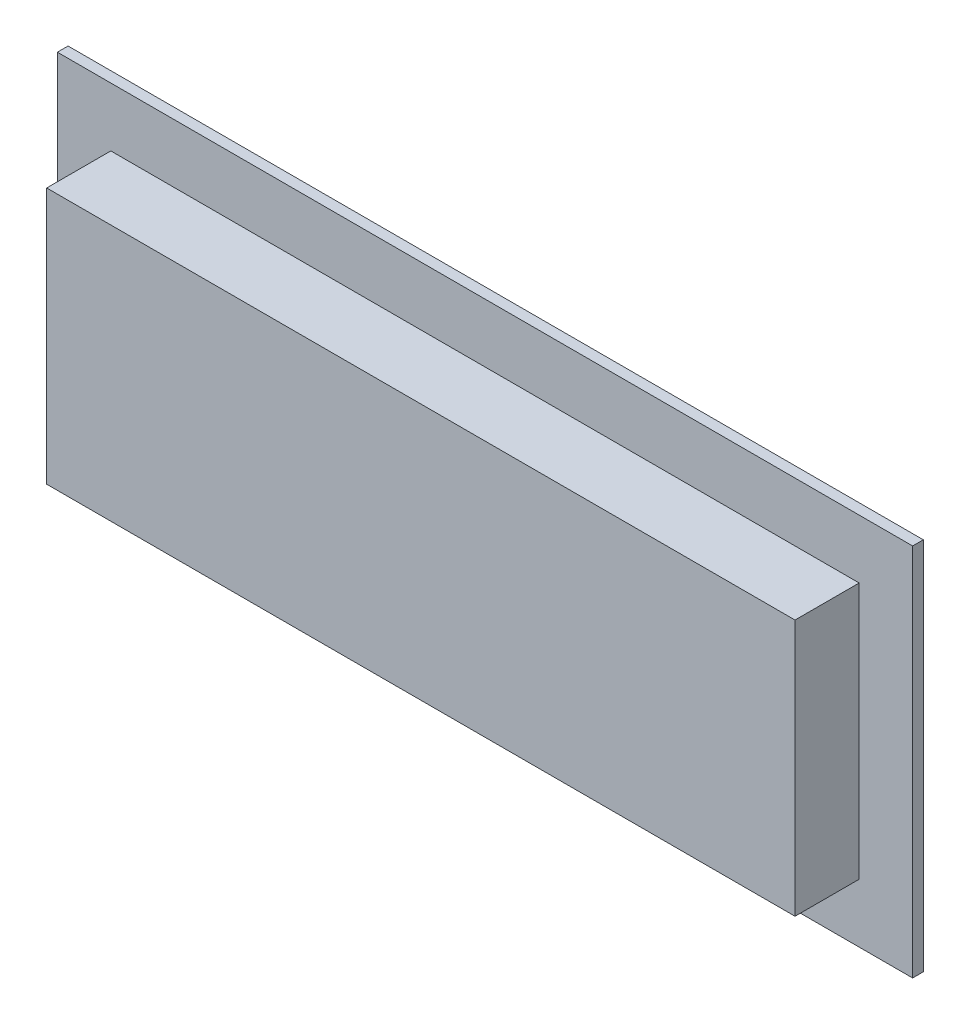
SolidWorks part; units mm, degrees
ref_plane "Front Plane" through (0, 0, 0) normal (0, 0, 1) x (1, 0, 0)
ref_plane "Top Plane" through (0, 0, 0) normal (0, 1, 0) x (1, 0, 0)
ref_plane "Right Plane" through (0, 0, 0) normal (1, 0, 0) x (0, 0, -1)
sketch "Sketch1" plane through (0, 0, 0) normal (0, 0, 1) x (1, 0, 0)
  line L1 (-40, -17.5) -> (40, -17.5)
  line L2 (-40, -17.5) -> (-40, 17.5)
  line L3 (-40, 17.5) -> (40, 17.5)
  line L4 (40, -17.5) -> (40, 17.5)
  line L5 (-40, -17.5) -> (40, 17.5) construction
  line L6 (-40, 17.5) -> (40, -17.5) construction
  point P0 (0, 0)
  dimension "D1" = 80
  dimension "D2" = 35
extrude "Boss-Extrude1" add sketch "Sketch1" along normal blind 1
sketch "Sketch2" plane through (0, 0, 1) normal (0, 0, 1) x (1, 0, 0)
  line L1 (-35, 12) -> (35, 12)
  line L2 (-35, 12) -> (-35, -12)
  line L3 (-35, -12) -> (35, -12)
  line L4 (35, 12) -> (35, -12)
  line L5 (-35, 12) -> (35, -12) construction
  line L6 (-35, -12) -> (35, 12) construction
  point P0 (0, 0)
  dimension "D1" = 24
  dimension "D2" = 70
extrude "Boss-Extrude2" add sketch "Sketch2" along normal blind 6
sketch "Sketch3" plane through (0, 0, 0) normal (0, 0, -1) x (-1, 0, 0)
  line L1 (8.4194, 0) -> (-36.2288, 0)
  line L2 (8.4194, 0) -> (8.4194, -14.8614)
  line L3 (8.4194, -14.8614) -> (-36.2288, -14.8614)
  line L4 (-36.2288, 0) -> (-36.2288, -14.8614)
extrude "Boss-Extrude3" add sketch "Sketch3" along normal blind 3
sketch "Sketch4" plane through (36.2288, 0, 0) normal (1, 0, 0) x (0, 0, -1)
  line L0 (0, 0) -> (0, -14.8614) construction
  line L1 (0, -13.6614) -> (2, -13.6614)
  line L2 (0, -13.6614) -> (0, 0.5343)
  line L3 (0, 0.5343) -> (2, 0.5343)
  line L4 (2, -13.6614) -> (2, 0.5343)
  line L5 (3, 0) -> (3, -14.8614) construction
  line L6 (3, -14.8614) -> (0, -14.8614) construction
  dimension "D1" = 1
  dimension "D2" = 1.2
extrude "Cut-Extrude1" cut sketch "Sketch4" against normal through all
sketch "Sketch5" plane through (0, 0, -3) normal (0, 0, -1) x (-1, 0, 0)
  line L1 (-12.1188, -3.5081) -> (-16.0733, -3.5081)
  line L2 (-12.1188, -3.5081) -> (-12.1188, -12.1826)
  line L3 (-12.1188, -12.1826) -> (-16.0733, -12.1826)
  line L4 (-16.0733, -3.5081) -> (-16.0733, -12.1826)
extrude "Boss-Extrude4" add sketch "Sketch5" along normal blind 1
